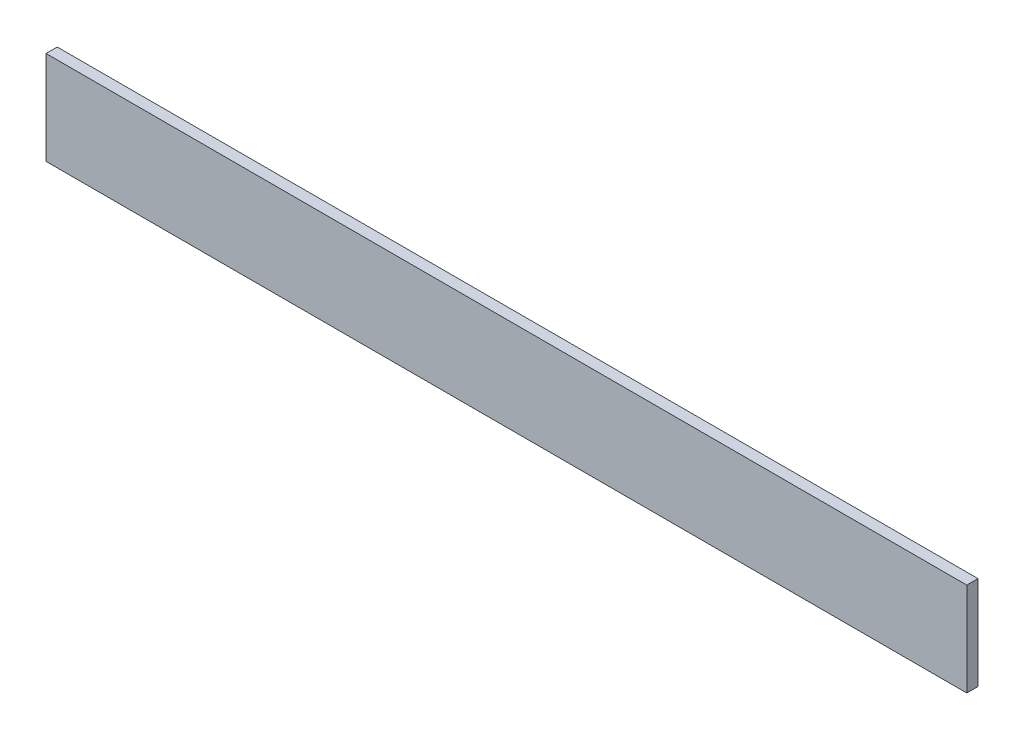
SolidWorks part; units mm, degrees
ref_plane "Alzado" through (0, 0, 0) normal (0, 0, 1) x (1, 0, 0)
ref_plane "Planta" through (0, 0, 0) normal (0, 1, 0) x (1, 0, 0)
ref_plane "Vista lateral" through (0, 0, 0) normal (1, 0, 0) x (0, 0, -1)
sketch "Croquis1" plane through (0, 0, 0) normal (0, 0, 1) x (1, 0, 0)
  line L0 (0, 0) -> (0, 100)
  line L1 (0, 100) -> (985, 100)
  line L2 (985, 100) -> (985, 0)
  line L3 (985, 0) -> (0, 0)
  dimension "D1" = 985
  dimension "D2" = 100
extrude "Saliente-Extruir1" add sketch "Croquis1" along normal blind 12
